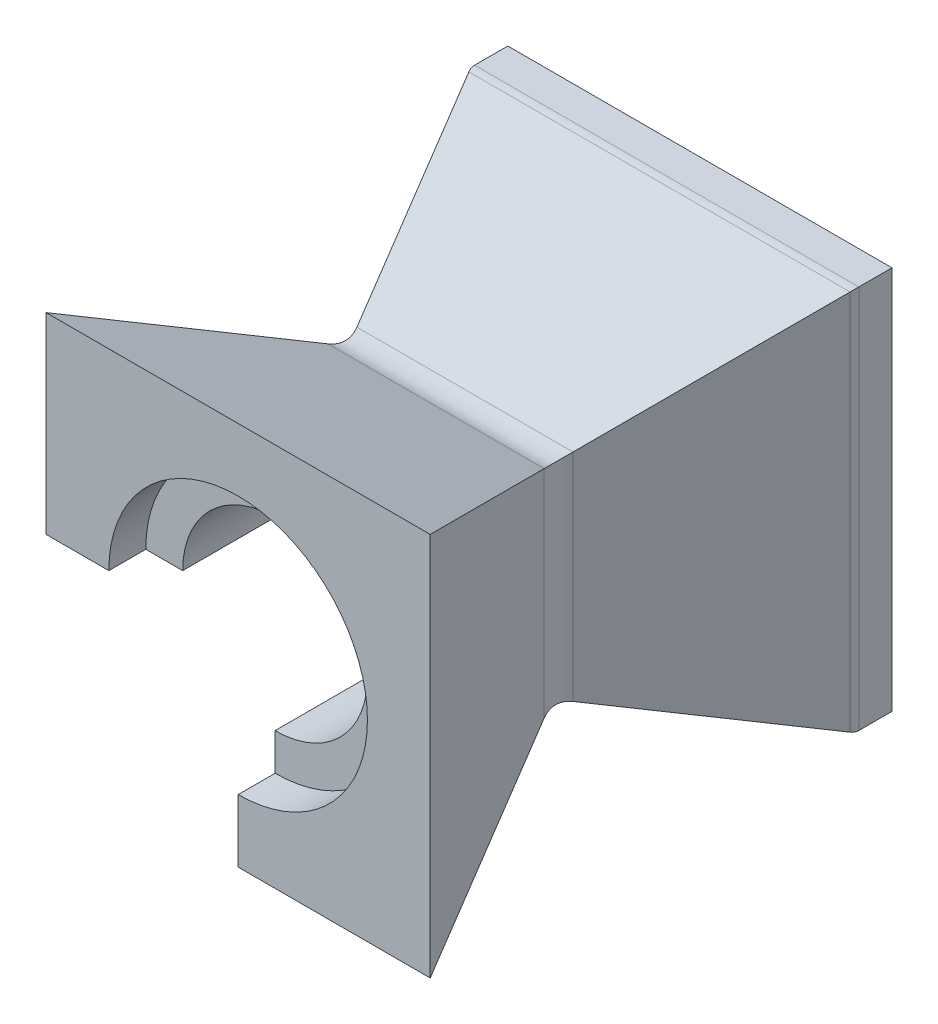
SolidWorks part; units mm, degrees
material "Cast Stainless Steel"
ref_plane "Front Plane" through (0, 0, 0) normal (0, 0, 1) x (1, 0, 0)
ref_plane "Top Plane" through (0, 0, 0) normal (0, 1, 0) x (1, 0, 0)
ref_plane "Right Plane" through (0, 0, 0) normal (1, 0, 0) x (0, 0, -1)
sketch "Sketch1" plane through (0, 0, 0) normal (0, 0, 1) x (1, 0, 0)
  line L1 (52, -52) -> (-52, -52)
  line L2 (52, -52) -> (52, 52)
  line L3 (52, 52) -> (-52, 52)
  line L4 (-52, -52) -> (-52, 52)
  line L5 (52, -52) -> (-52, 52) construction
  line L6 (52, 52) -> (-52, -52) construction
  circle A0 centre (0, 0) radius 25
  point P0 (0, 0)
  dimension "D3" = 50
  dimension "D1" = 104
  dimension "D2" = 104
extrude "Boss-Extrude1" add sketch "Sketch1" along normal blind 115
sketch "Sketch4" plane through (0, 52, 0) normal (0, 1, 0) x (1, 0, 0)
  line L0 (0, 0) -> (0, -115) construction
  line L1 (52, -115) -> (-52, -115) construction
  line L2 (-52, -57.5) -> (52, -57.5) construction
  line L3 (-52, -115) -> (-52, 0) construction
  line L4 (52, -115) -> (52, 0) construction
  line L5 (-52, 0) -> (-27.5927, -57.5)
  line L6 (-52, 0) -> (-52, -115)
  line L7 (-52, -115) -> (-27.5927, -57.5)
  line L8 (52, -115) -> (27.5927, -57.5)
  line L9 (52, 0) -> (52, -115)
  line L10 (52, 0) -> (27.5927, -57.5)
  dimension "D1" = 23
sketch "Sketch7" plane through (-52, 0, 0) normal (-1, 0, 0) x (0, 0, 1)
  line L0 (0, 0) -> (115, 0) construction
  line L1 (115, 52) -> (115, -52) construction
  line L2 (57.5, 52) -> (57.5, -52) construction
  line L3 (0, 52) -> (115, 52) construction
  line L4 (115, -52) -> (0, -52) construction
  line L5 (0, 52) -> (115, 52)
  line L6 (115, 52) -> (57.5, 27.5927)
  line L7 (57.5, 27.5927) -> (0, 52)
  line L8 (0, -52) -> (115, -52)
  line L9 (57.5, -27.5927) -> (0, -52)
  line L10 (115, -52) -> (57.5, -27.5927)
  dimension "D1" = 23
extrude "Cut-Extrude3" cut sketch "Sketch7" against normal blind 115
extrude "Cut-Extrude4" cut sketch "Sketch4" against normal blind 115
sketch "Sketch8" plane through (0, 0, 0) normal (0, 0, -1) x (-1, 0, 0)
  line L0 (0, 0) -> (96.3898, 0)
  line L1 (0, 0) -> (0, -95.4247)
  arc A0 (96.3898, 0) -> (0, -95.4247) centre (33.5026, -32.8715) cw
extrude "Cut-Extrude5" cut sketch "Sketch8" against normal through all
fillet "Fillet1" radius 10 4 edges at (13.7963, -27.5927, 57.5) (27.5927, 0, 57.5) (0, 27.5927, 57.5) (-27.5927, 13.7963, 57.5)
sketch "Sketch9" plane through (0, 0, 0) normal (0, 0, -1) x (-1, 0, 0)
  circle A0 centre (0, 0) radius 35
  dimension "D1" = 70
extrude "Cut-Extrude6" cut sketch "Sketch9" against normal blind 10
sketch "Sketch10" plane through (0, 0, 115) normal (0, 0, 1) x (1, 0, 0)
  circle A0 centre (0, 0) radius 35
  dimension "D1" = 70
extrude "Cut-Extrude7" cut sketch "Sketch10" against normal blind 10
sketch "Sketch11" plane through (0, 0, 0) normal (0, 0, -1) x (-1, 0, 0)
  line L0 (52, 0) -> (52, 52)
  line L1 (52, 52) -> (-52, 52)
  line L2 (-52, 52) -> (-52, -52)
  line L3 (-52, -52) -> (0, -52)
  line L4 (49, 0) -> (49, 49)
  line L5 (49, 49) -> (-49, 49)
  line L6 (-49, 49) -> (-49, -49)
  line L7 (-49, -49) -> (0, -49)
  line L8 (0, -49) -> (0, -52)
  line L9 (49, 0) -> (52, 0)
  dimension "D1" = 3
extrude "Boss-Extrude2" add sketch "Sketch11" along normal blind 10
fillet "Fillet2" radius 5 4 edges at (-52, 26, 0) (0, 52, 0) (26, -52, 0) (52, 0, 0)
sketch "Sketch12" plane through (0, 0, 0) normal (0, 0, -1) x (-1, 0, 0)
  line L0 (-49, 49) -> (0, 0) construction
  line L1 (-49, -49) -> (49, 49) construction
  line L2 (30.052, 30.052) -> (40.6586, 40.6586) construction
  line L3 (27.9307, 32.1734) -> (38.5373, 42.78)
  line L4 (32.1734, 27.9307) -> (42.78, 38.5373)
  line L5 (-30.052, 30.052) -> (-40.6586, 40.6586) construction
  line L6 (-32.1734, 27.9307) -> (-42.78, 38.5373)
  line L7 (-27.9307, 32.1734) -> (-38.5373, 42.78)
  line L8 (-30.052, -30.052) -> (-40.6586, -40.6586) construction
  line L9 (-27.9307, -32.1734) -> (-38.5373, -42.78)
  line L10 (-32.1734, -27.9307) -> (-42.78, -38.5373)
  circle A0 centre (0, 0) radius 50 construction
  arc A1 (27.9307, 32.1734) -> (32.1734, 27.9307) centre (30.052, 30.052) ccw
  arc A2 (42.78, 38.5373) -> (38.5373, 42.78) centre (40.6586, 40.6586) ccw
  arc A3 (-32.1734, 27.9307) -> (-27.9307, 32.1734) centre (-30.052, 30.052) ccw
  arc A4 (-38.5373, 42.78) -> (-42.78, 38.5373) centre (-40.6586, 40.6586) ccw
  arc A5 (-27.9307, -32.1734) -> (-32.1734, -27.9307) centre (-30.052, -30.052) ccw
  arc A6 (-42.78, -38.5373) -> (-38.5373, -42.78) centre (-40.6586, -40.6586) ccw
  point P11 (35.3553, 35.3553)
  point P16 (-35.3553, 35.3553)
  point P23 (-35.3553, -35.3553)
  point P30 (-35.3553, -35.3553)
  dimension "D1" = 100
  dimension "D2" = 3
  dimension "D5" = 3
  dimension "D6" = 3
  dimension "D3" = 15
  dimension "D4" = 15
  dimension "D7" = 15
extrude "Cut-Extrude8" cut sketch "Sketch12" against normal blind 10
equation "\"A\"= 115mm"
equation "\"B\"= 104mm"
equation "\"C\"= 23mm"
